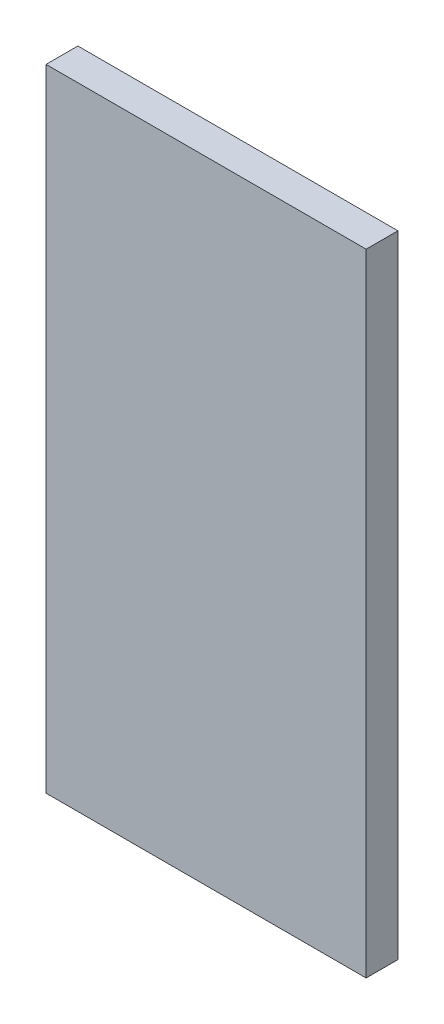
SolidWorks part; units mm, degrees
ref_plane "正面" through (0, 0, 0) normal (0, 0, 1) x (1, 0, 0)
ref_plane "平面" through (0, 0, 0) normal (0, 1, 0) x (1, 0, 0)
ref_plane "右側面" through (0, 0, 0) normal (1, 0, 0) x (0, 0, -1)
sketch "ｽｹｯﾁ1" plane through (0, 0, 0) normal (0, 0, 1) x (1, 0, 0)
  line L3 (-34.7342, 40.4551) -> (42.6458, 40.4551)
  line L4 (-34.7342, 40.4551) -> (-34.7342, -112.1349)
  line L5 (-34.7342, -112.1349) -> (42.6458, -112.1349)
  line L6 (42.6458, 40.4551) -> (42.6458, -112.1349)
  dimension "D1" = 77.38
  dimension "D2" = 152.59
extrude "ﾎﾞｽ - 押し出し1" add sketch "ｽｹｯﾁ1" along normal blind 7.69
